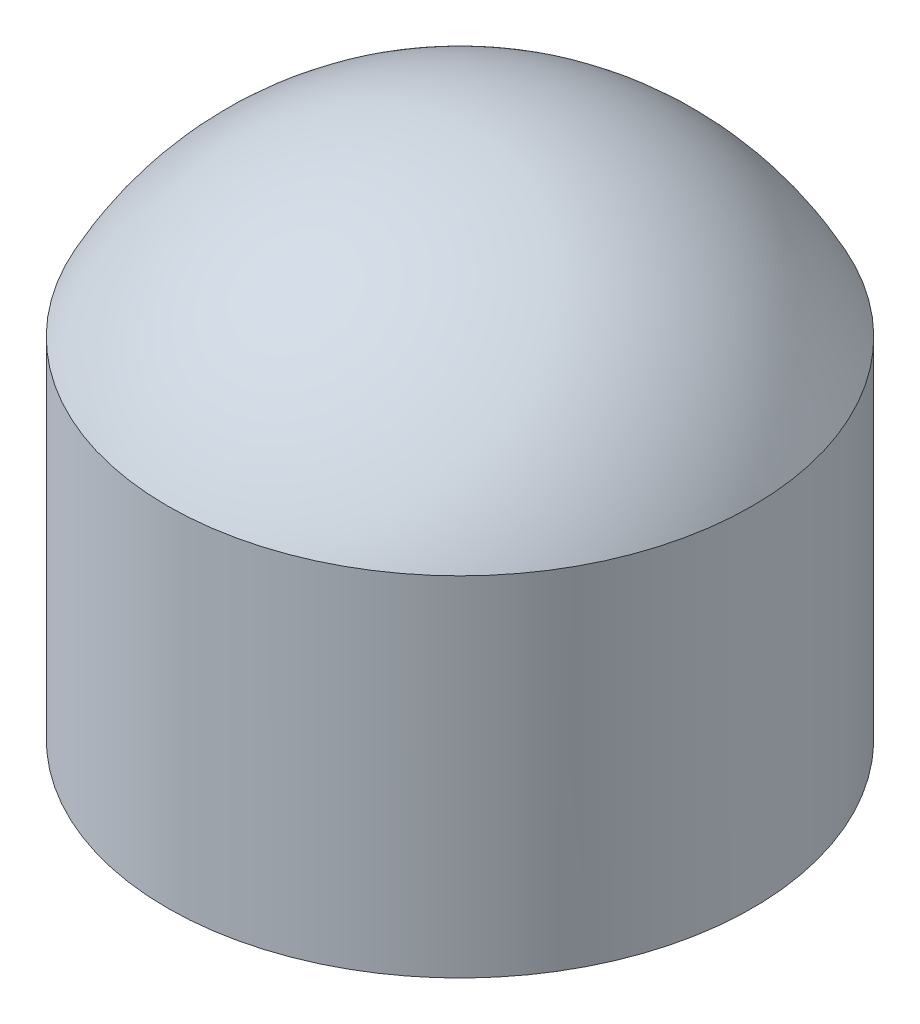
SolidWorks part; units mm, degrees
ref_plane "Front Plane" through (0, 0, 0) normal (0, 0, 1) x (1, 0, 0)
ref_plane "Top Plane" through (0, 0, 0) normal (0, 1, 0) x (1, 0, 0)
ref_plane "Right Plane" through (0, 0, 0) normal (1, 0, 0) x (0, 0, -1)
sketch "Sketch1" plane through (0, 0, 0) normal (0, 1, 0) x (1, 0, 0)
  circle A0 centre (0, 0) radius 28.2067
  dimension "D1" = 56.4134
extrude "Boss-Extrude1" add sketch "Sketch1" along normal blind 33.5788
sketch "Sketch2" plane through (0, 0, 0) normal (0, 0, 1) x (1, 0, 0)
  line L0 (28.2067, 33.5788) -> (-28.2067, 33.5788) construction
  line L1 (0, 33.5788) -> (-28.2067, 33.5788)
  line L2 (0, 33.5788) -> (0, 50.7533) construction
  line L3 (0, 50.7533) -> (-17.717, 50.7533) construction
  line L4 (0, 50.7533) -> (0, 33.5788)
  arc A0 (0, 50.7533) -> (-28.2067, 33.5788) centre (0, 19.0033) ccw
  dimension "D1" = 31.75
revolve "Revolve1" add sketch "Sketch2" angle 360 about L4
shell "Shell1" thickness 4.064
